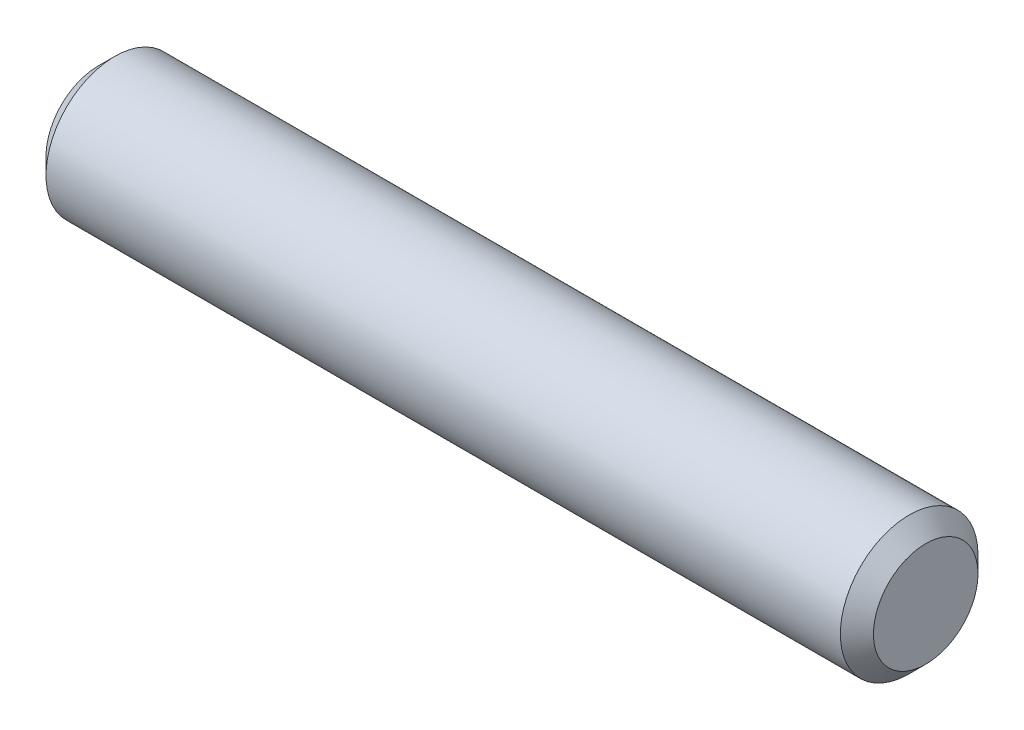
SolidWorks part; units mm, degrees
material "Plain Carbon Steel"
ref_plane "Front Plane" through (0, 0, 0) normal (0, 0, 1) x (1, 0, 0)
ref_plane "Top Plane" through (0, 0, 0) normal (0, 1, 0) x (1, 0, 0)
ref_plane "Right Plane" through (0, 0, 0) normal (1, 0, 0) x (0, 0, -1)
sketch "Sketch1" plane through (0, 0, 0) normal (1, 0, 0) x (0, 0, -1)
  circle A0 centre (0, 0) radius 6.3373
  dimension "D1" = 12.6746
extrude "Boss-Extrude1" add sketch "Sketch1" along normal mid plane 76.2
chamfer "Chamfer1" distance 1.524 angle 45 1 edges at (38.1, 0, -6.3373)
chamfer "Chamfer2" distance 1.524 angle 45 1 edges at (-38.1, 0, -6.3373)
